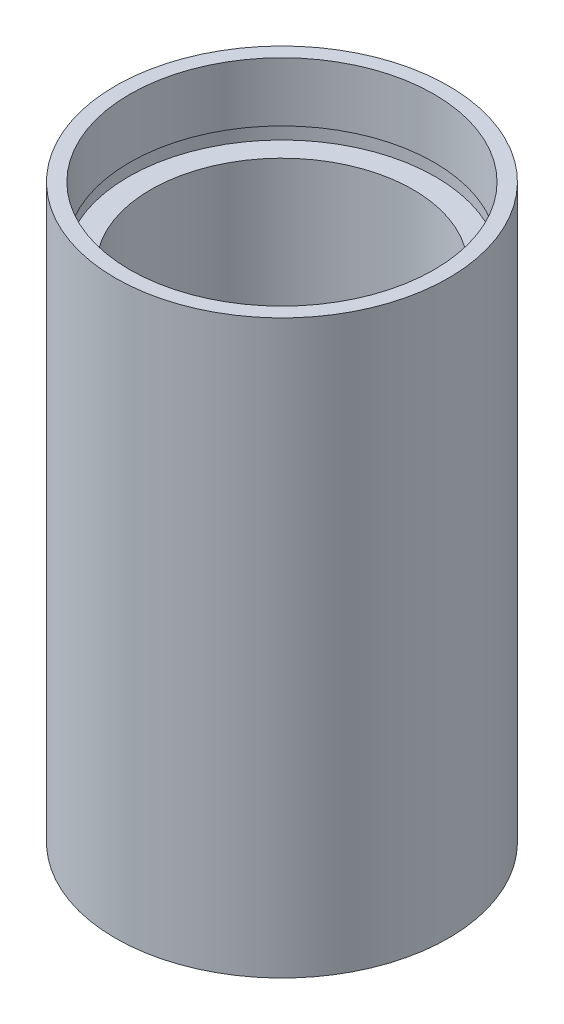
SolidWorks part; units mm, degrees
ref_plane "前视基准面" through (0, 0, 0) normal (0, 0, 1) x (1, 0, 0)
ref_plane "上视基准面" through (0, 0, 0) normal (0, 1, 0) x (1, 0, 0)
ref_plane "右视基准面" through (0, 0, 0) normal (1, 0, 0) x (0, 0, -1)
sketch "草图1" plane through (0, 0, 0) normal (0, 0, 1) x (1, 0, 0)
  line L0 (0, 161.3762) -> (0, 0) construction
  line L1 (141.7365, 0) -> (-131.7984, 0) construction
  line L2 (11.1, 0) -> (11.1, 4.5)
  line L3 (11.7, 4.5) -> (11.7, 5.5)
  line L4 (11.1, 4.5) -> (11.7, 4.5)
  line L5 (10, 5.5) -> (10, 38.1)
  line L6 (11.7, 5.5) -> (10, 5.5)
  line L7 (12.7, 0) -> (12.7, 43.6)
  line L8 (11.1, 0) -> (12.7, 0)
  line L9 (11.6, 43.6) -> (11.6, 39.1)
  line L10 (11.6, 43.6) -> (12.7, 43.6)
  line L11 (11.7, 39.1) -> (11.7, 38.1)
  line L12 (11.6, 39.1) -> (11.7, 39.1)
  line L13 (10, 38.1) -> (11.7, 38.1)
  point P15 (11.6, 41.35)
  dimension "D1" = 11.1
  dimension "D2" = 4.5
  dimension "D3" = 11.7
  dimension "D4" = 10
  dimension "D5" = 12.7
  dimension "D6" = 11.6
  dimension "D7" = 4.5
  dimension "D8" = 11.7
  dimension "D9" = 5.5
  dimension "D10" = 1
  dimension "D11" = 38.1
revolve "旋转1" add sketch "草图1" angle 360 about L0
cosmetic thread "装饰螺纹线1"
cosmetic thread "装饰螺纹线2"
cosmetic thread "装饰螺纹线3"
